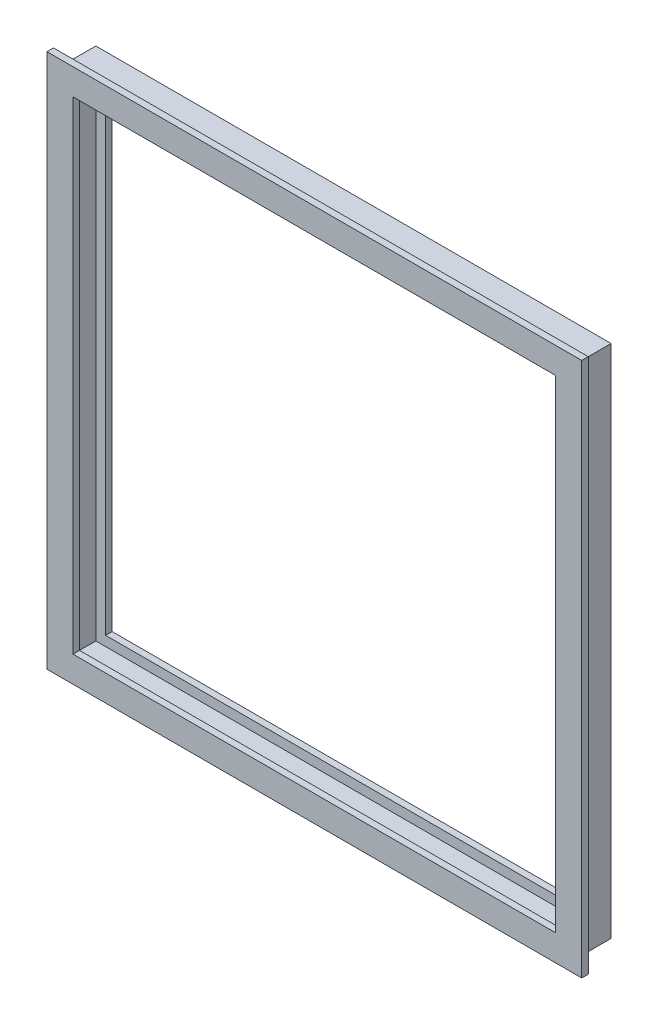
SolidWorks part; units mm, degrees
material "ABS"
ref_plane "Front Plane" through (0, 0, 0) normal (0, 0, 1) x (1, 0, 0)
ref_plane "Top Plane" through (0, 0, 0) normal (0, 1, 0) x (1, 0, 0)
ref_plane "Right Plane" through (0, 0, 0) normal (1, 0, 0) x (0, 0, -1)
sketch "Sketch1" plane through (0, 0, 0) normal (0, 1, 0) x (1, 0, 0)
  line L0 (-125.4125, 7.9375) -> (-125.4125, -7.9375)
  line L1 (-125.4125, -7.9375) -> (-130.175, -7.9375)
  line L2 (-130.175, -7.9375) -> (-130.175, -11.1125)
  line L3 (-130.175, -11.1125) -> (-117.475, -11.1125)
  line L4 (-117.475, -11.1125) -> (-117.475, -7.9375)
  line L5 (-117.475, -7.9375) -> (-122.2375, -7.9375)
  line L6 (-122.2375, -7.9375) -> (-122.2375, 4.7625)
  line L7 (-122.2375, 4.7625) -> (-117.475, 4.7625)
  line L8 (-117.475, 4.7625) -> (-117.475, 7.9375)
  line L9 (-117.475, 7.9375) -> (-125.4125, 7.9375)
  point P7 (-125.4125, 0)
  dimension "D1" = 19.05
  dimension "D2" = 12.7
  dimension "D3" = 3.175
  dimension "D4" = 4.7625
  dimension "D5" = 12.7
  dimension "D6" = 3.175
  dimension "D7" = 125.4125
sketch "Sketch2" plane through (0, 0, 0) normal (0, 0, 1) x (1, 0, 0)
  line L1 (125.4125, -125.4125) -> (-125.4125, -125.4125)
  line L2 (125.4125, -125.4125) -> (125.4125, 125.4125)
  line L3 (125.4125, 125.4125) -> (-125.4125, 125.4125)
  line L4 (-125.4125, -125.4125) -> (-125.4125, 125.4125)
  line L5 (125.4125, -125.4125) -> (-125.4125, 125.4125) construction
  line L6 (125.4125, 125.4125) -> (-125.4125, -125.4125) construction
  point P0 (0, 0)
  dimension "D1" = 250.825
  dimension "D2" = 250.825
sweep "Sweep1" add profiles "Sketch1" path "Sketch2"
